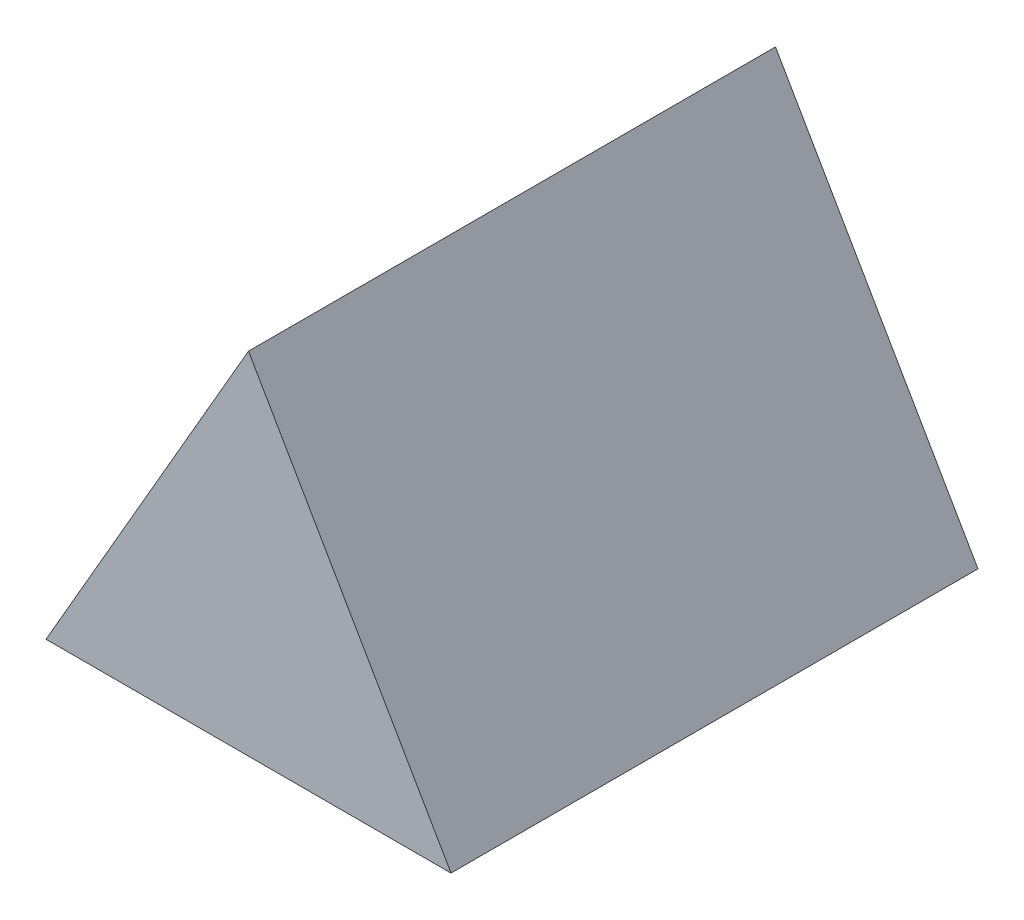
SolidWorks part; units mm, degrees
ref_plane "Piano frontale" through (0, 0, 0) normal (0, 0, 1) x (1, 0, 0)
ref_plane "Piano superiore" through (0, 0, 0) normal (0, 1, 0) x (1, 0, 0)
ref_plane "Piano destro" through (0, 0, 0) normal (1, 0, 0) x (0, 0, -1)
sketch "Schizzo1" plane through (0, 0, 0) normal (0, 0, 1) x (1, 0, 0)
  line L1 (0, 71) -> (-61.4878, -35.5)
  line L2 (-61.4878, -35.5) -> (61.4878, -35.5)
  line L3 (61.4878, -35.5) -> (0, 71)
  circle A0 centre (0, 0) radius 35.5 construction
  dimension "D1" = 71
extrude "Estrusione-Estrusione1" add sketch "Schizzo1" along normal blind 160
